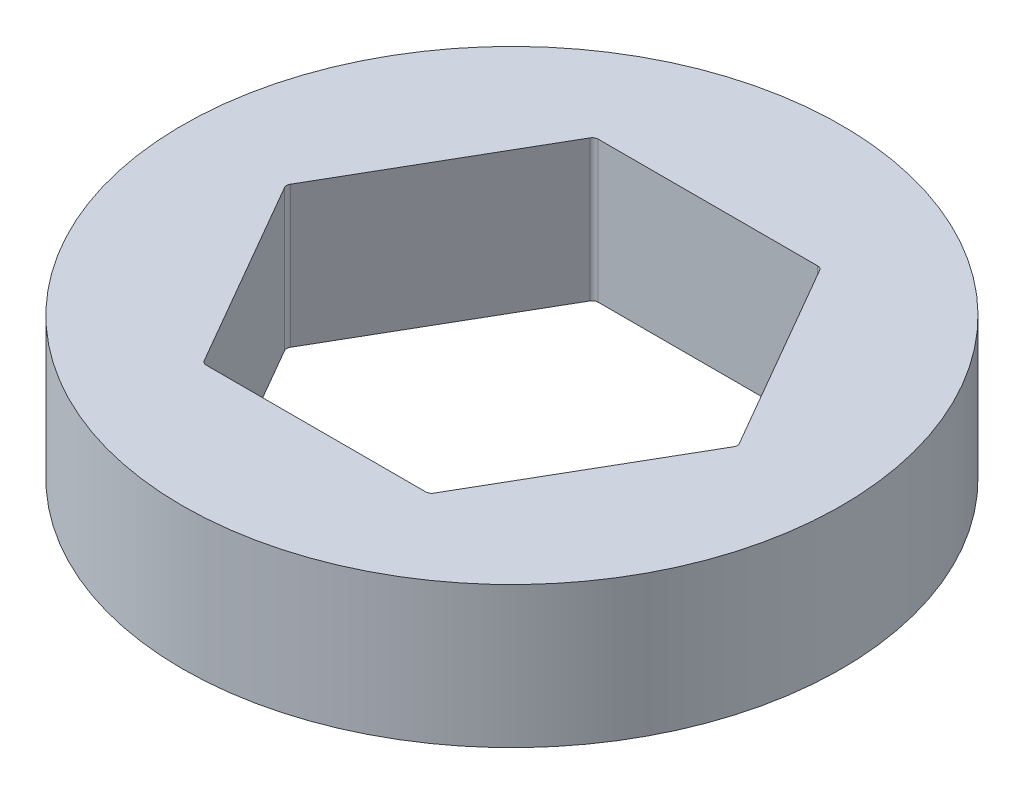
SolidWorks part; units mm, degrees
material "Nylon 101"
ref_plane "Front Plane" through (0, 0, 0) normal (0, 0, 1) x (1, 0, 0)
ref_plane "Top Plane" through (0, 0, 0) normal (0, 1, 0) x (1, 0, 0)
ref_plane "Right Plane" through (0, 0, 0) normal (1, 0, 0) x (0, 0, -1)
sketch "Sketch1" plane through (0, 0, 0) normal (0, 1, 0) x (1, 0, 0)
  line L1 (7.6256, 0) -> (3.8128, 6.604)
  line L2 (3.8128, 6.604) -> (-3.8128, 6.604)
  line L3 (-3.8128, 6.604) -> (-7.6256, 0)
  line L4 (-7.6256, 0) -> (-3.8128, -6.604)
  line L5 (-3.8128, -6.604) -> (3.8128, -6.604)
  line L6 (3.8128, -6.604) -> (7.6256, 0)
  circle A0 centre (0, 0) radius 11.1125
  circle A1 centre (0, 0) radius 6.604 construction
  dimension "D1" = 13.208
  dimension "D2" = 22.225
extrude "Boss-Extrude1" add sketch "Sketch1" along normal blind 4.7625
fillet "Fillet1" radius 0.2 6 edges at (3.8128, 2.3813, -6.604) (-3.8128, 2.3813, -6.604) (-7.6256, 2.3813, 0) (3.8128, 2.3813, 6.604) (7.6256, 2.3813, 0) (-3.8128, 2.3813, 6.604)
